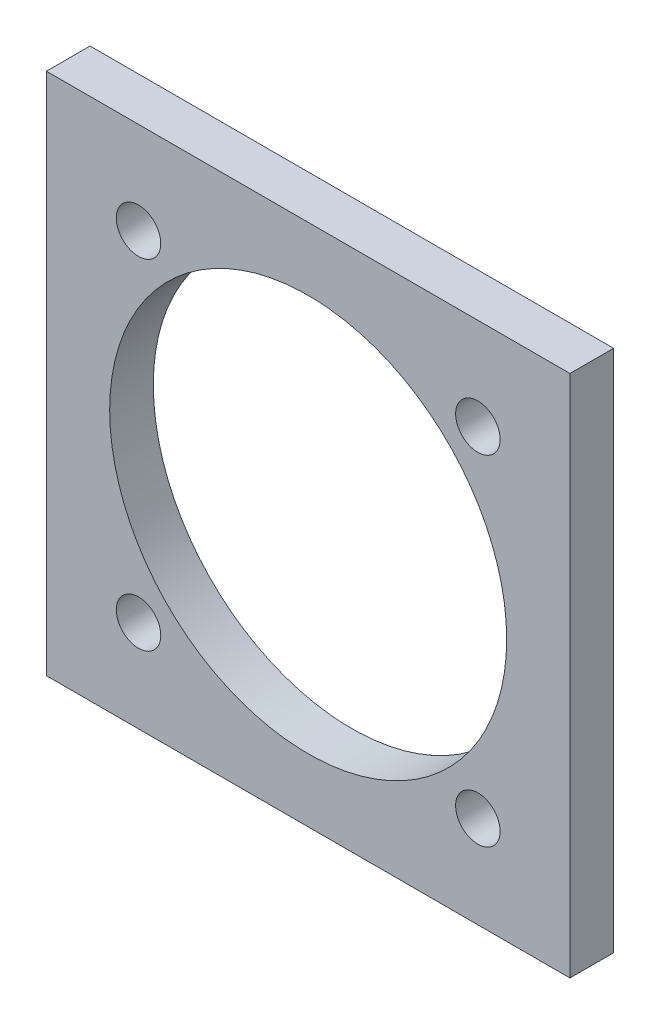
SolidWorks part; units mm, degrees
ref_plane "Ön Düzlem" through (0, 0, 0) normal (0, 0, 1) x (1, 0, 0)
ref_plane "Üst Düzlem" through (0, 0, 0) normal (0, 1, 0) x (1, 0, 0)
ref_plane "Sağ Düzlem" through (0, 0, 0) normal (1, 0, 0) x (0, 0, -1)
sketch "Çizim1" plane through (0, 0, 0) normal (0, 0, 1) x (1, 0, 0)
  line L0 (-38.8909, 38.8909) -> (38.8909, 38.8909) construction
  line L1 (-38.8909, 38.8909) -> (-38.8909, -38.8909) construction
  line L2 (-38.8909, -38.8909) -> (38.8909, -38.8909) construction
  line L3 (38.8909, 38.8909) -> (38.8909, -38.8909) construction
  line L4 (-38.8909, 38.8909) -> (38.8909, -38.8909) construction
  line L5 (-38.8909, -38.8909) -> (38.8909, 38.8909) construction
  line L6 (-60, -60) -> (60, -60)
  line L7 (-60, -60) -> (-60, 60)
  line L8 (-60, 60) -> (60, 60)
  line L9 (60, -60) -> (60, 60)
  line L10 (-60, -60) -> (60, 60) construction
  line L11 (-60, 60) -> (60, -60) construction
  circle A0 centre (0, 0) radius 45.5
  circle A1 centre (-38.8909, 38.8909) radius 5.1
  circle A2 centre (38.8909, 38.8909) radius 5.1
  circle A3 centre (38.8909, -38.8909) radius 5.1
  circle A4 centre (-38.8909, -38.8909) radius 5.1
  circle A5 centre (0, 0) radius 55 construction
  point P3 (12.4041, -2.058)
  dimension "D1" = 91
  dimension "D2" = 110
  dimension "D3" = 10.2
  dimension "D4" = 120
extrude "Yükseklik-Ekstrüzyon1" add sketch "Çizim1" along normal blind 10
